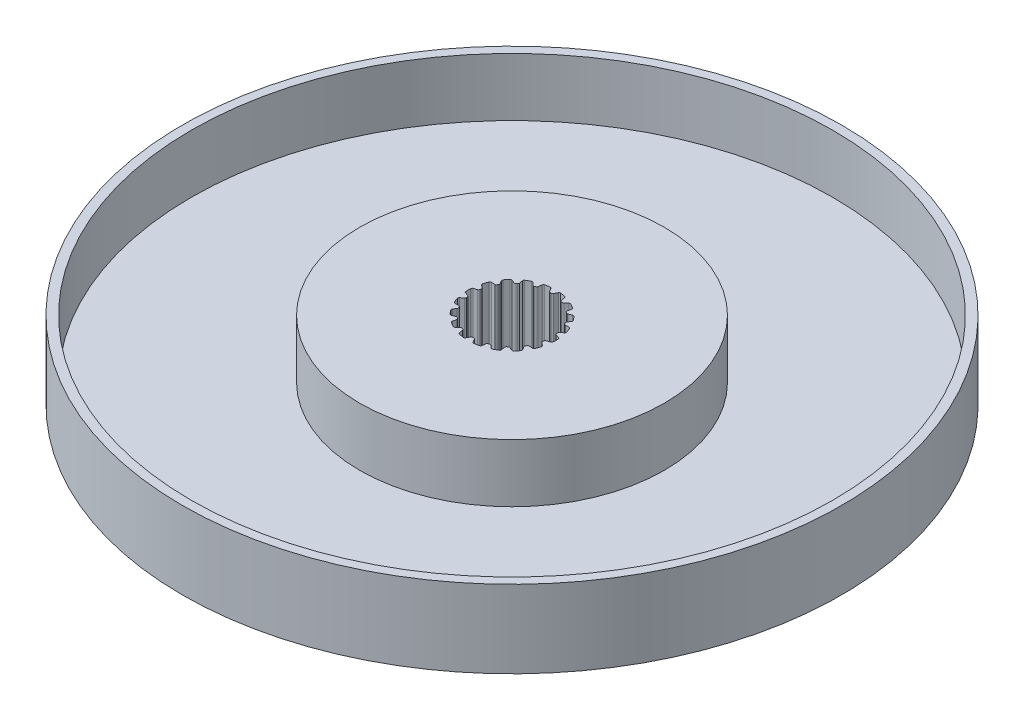
SolidWorks part; units mm, degrees
ref_plane "Front Plane" through (0, 0, 0) normal (0, 0, 1) x (1, 0, 0)
ref_plane "Top Plane" through (0, 0, 0) normal (0, 1, 0) x (1, 0, 0)
ref_plane "Right Plane" through (0, 0, 0) normal (1, 0, 0) x (0, 0, -1)
sketch "Sketch1" plane through (0, 0, 0) normal (0, 1, 0) x (1, 0, 0)
  circle A0 centre (0, 0) radius 42.5
  dimension "D1" = 85
extrude "Boss-Extrude1" add sketch "Sketch1" along normal blind 10
sketch "Sketch2" plane through (0, 10, 10) normal (0, 1, 0) x (1, 0, 0)
  line L1 (-5.2151, 8.5153) -> (-4.9419, 8.7287)
  line L3 (-5.0787, 9.5044) -> (-5.4084, 9.6115)
  line L5 (-5.4084, 10.3885) -> (-5.0787, 10.4956)
  line L7 (-4.9419, 11.2713) -> (-5.2151, 11.4847)
  line L9 (-4.9493, 12.2148) -> (-4.6029, 12.2027)
  line L11 (-4.2091, 12.8848) -> (-4.3928, 13.1788)
  line L13 (-3.8933, 13.774) -> (-3.5719, 13.6442)
  line L15 (-2.9686, 14.1504) -> (-3.0406, 14.4895)
  line L17 (-2.3677, 14.878) -> (-2.1101, 14.6461)
  line L19 (-1.37, 14.9154) -> (-1.3217, 15.2587)
  line L21 (-0.5566, 15.3937) -> (-0.3938, 15.0876)
  line L23 (0.3938, 15.0876) -> (0.5566, 15.3937)
  line L25 (1.3217, 15.2587) -> (1.37, 14.9154)
  line L27 (2.1101, 14.6461) -> (2.3677, 14.878)
  line L29 (3.0406, 14.4895) -> (2.9686, 14.1504)
  line L31 (3.5719, 13.6442) -> (3.8933, 13.774)
  line L33 (4.3928, 13.1788) -> (4.2091, 12.8848)
  line L35 (4.6029, 12.2027) -> (4.9493, 12.2148)
  line L37 (5.2151, 11.4847) -> (4.9419, 11.2713)
  line L39 (5.0787, 10.4956) -> (5.4084, 10.3885)
  line L41 (5.4084, 9.6115) -> (5.0787, 9.5044)
  line L43 (4.9419, 8.7287) -> (5.2151, 8.5153)
  line L45 (4.9493, 7.7852) -> (4.6029, 7.7973)
  line L47 (4.2091, 7.1152) -> (4.3928, 6.8212)
  line L49 (3.8933, 6.226) -> (3.5719, 6.3558)
  line L51 (2.9686, 5.8496) -> (3.0406, 5.5105)
  line L53 (2.3677, 5.122) -> (2.1101, 5.3539)
  line L55 (1.37, 5.0846) -> (1.3217, 4.7413)
  line L57 (0.5566, 4.6063) -> (0.3938, 4.9124)
  line L59 (-0.3938, 4.9124) -> (-0.5566, 4.6063)
  line L61 (-1.3217, 4.7413) -> (-1.37, 5.0846)
  line L63 (-2.1101, 5.3539) -> (-2.3677, 5.122)
  line L65 (-3.0406, 5.5105) -> (-2.9686, 5.8496)
  line L67 (-3.5719, 6.3558) -> (-3.8933, 6.226)
  line L69 (-4.3928, 6.8212) -> (-4.2091, 7.1152)
  line L71 (-4.6029, 7.7973) -> (-4.9493, 7.7852)
  circle A0 centre (0, 10) radius 42.5 construction
  arc A1 (-5.292, 8.2623) -> (-5.1709, 7.9295) centre (0, 10) ccw
  arc A3 (-5.2151, 8.5153) -> (-5.292, 8.2623) centre (-5.0735, 8.334) ccw
  arc A5 (-4.9419, 8.7287) -> (-4.8325, 9.0245) centre (-5.1266, 8.9651) ccw
  arc A7 (-4.8747, 9.2639) -> (-4.8325, 9.0245) centre (0, 10) ccw
  arc A9 (-4.8747, 9.2639) -> (-5.0787, 9.5044) centre (-5.1714, 9.2191) ccw
  arc A11 (-5.5672, 9.8229) -> (-5.4084, 9.6115) centre (-5.3373, 9.8302) ccw
  arc A13 (-5.5672, 10.1771) -> (-5.5672, 9.8229) centre (0, 10) ccw
  arc A15 (-5.4084, 10.3885) -> (-5.5672, 10.1771) centre (-5.3373, 10.1698) ccw
  arc A17 (-5.0787, 10.4956) -> (-4.8747, 10.7361) centre (-5.1714, 10.7809) ccw
  arc A19 (-4.8325, 10.9755) -> (-4.8747, 10.7361) centre (0, 10) ccw
  arc A21 (-4.8325, 10.9755) -> (-4.9419, 11.2713) centre (-5.1266, 11.0349) ccw
  arc A23 (-5.292, 11.7377) -> (-5.2151, 11.4847) centre (-5.0735, 11.666) ccw
  arc A25 (-5.1709, 12.0705) -> (-5.292, 11.7377) centre (0, 10) ccw
  arc A27 (-4.9493, 12.2148) -> (-5.1709, 12.0705) centre (-4.9574, 11.985) ccw
  arc A29 (-4.6029, 12.2027) -> (-4.329, 12.359) centre (-4.5924, 12.5026) ccw
  arc A31 (-4.2074, 12.5695) -> (-4.329, 12.359) centre (0, 10) ccw
  arc A33 (-4.2074, 12.5695) -> (-4.2091, 12.8848) centre (-4.4635, 12.7259) ccw
  arc A35 (-4.3785, 13.4429) -> (-4.3928, 13.1788) centre (-4.1977, 13.3007) ccw
  arc A37 (-4.1509, 13.7142) -> (-4.3785, 13.4429) centre (0, 10) ccw
  arc A39 (-3.8933, 13.774) -> (-4.1509, 13.7142) centre (-3.9795, 13.5608) ccw
  arc A41 (-3.5719, 13.6442) -> (-3.2611, 13.6973) centre (-3.4595, 13.9223) ccw
  arc A43 (-3.0749, 13.8536) -> (-3.2611, 13.6973) centre (0, 10) ccw
  arc A45 (-3.0749, 13.8536) -> (-2.9686, 14.1504) centre (-3.262, 14.0881) ccw
  arc A47 (-2.9369, 14.7328) -> (-3.0406, 14.4895) centre (-2.8157, 14.5374) ccw
  arc A49 (-2.6303, 14.9099) -> (-2.9369, 14.7328) centre (0, 10) ccw
  arc A51 (-2.3677, 14.878) -> (-2.6303, 14.9099) centre (-2.5216, 14.7071) ccw
  arc A53 (-2.1101, 14.6461) -> (-1.7998, 14.5897) centre (-1.9094, 14.869) ccw
  arc A55 (-1.5714, 14.6728) -> (-1.7998, 14.5897) centre (0, 10) ccw
  arc A57 (-1.5714, 14.6728) -> (-1.37, 14.9154) centre (-1.6671, 14.9572) ccw
  arc A59 (-1.1411, 15.4519) -> (-1.3217, 15.2587) centre (-1.094, 15.2267) ccw
  arc A61 (-0.7924, 15.5134) -> (-1.1411, 15.4519) centre (0, 10) ccw
  arc A63 (-0.5566, 15.3937) -> (-0.7924, 15.5134) centre (-0.7596, 15.2857) ccw
  arc A65 (-0.3938, 15.0876) -> (-0.1215, 14.9285) centre (-0.1289, 15.2284) ccw
  arc A67 (0.1215, 14.9285) -> (-0.1215, 14.9285) centre (0, 10) ccw
  arc A69 (0.1215, 14.9285) -> (0.3938, 15.0876) centre (0.1289, 15.2284) ccw
  arc A71 (0.7924, 15.5134) -> (0.5566, 15.3937) centre (0.7596, 15.2857) ccw
  arc A73 (1.1411, 15.4519) -> (0.7924, 15.5134) centre (0, 10) ccw
  arc A75 (1.3217, 15.2587) -> (1.1411, 15.4519) centre (1.094, 15.2267) ccw
  arc A77 (1.37, 14.9154) -> (1.5714, 14.6728) centre (1.6671, 14.9572) ccw
  arc A79 (1.7998, 14.5897) -> (1.5714, 14.6728) centre (0, 10) ccw
  arc A81 (1.7998, 14.5897) -> (2.1101, 14.6461) centre (1.9094, 14.869) ccw
  arc A83 (2.6303, 14.9099) -> (2.3677, 14.878) centre (2.5216, 14.7071) ccw
  arc A85 (2.9369, 14.7328) -> (2.6303, 14.9099) centre (0, 10) ccw
  arc A87 (3.0406, 14.4895) -> (2.9369, 14.7328) centre (2.8157, 14.5374) ccw
  arc A89 (2.9686, 14.1504) -> (3.0749, 13.8536) centre (3.262, 14.0881) ccw
  arc A91 (3.2611, 13.6973) -> (3.0749, 13.8536) centre (0, 10) ccw
  arc A93 (3.2611, 13.6973) -> (3.5719, 13.6442) centre (3.4595, 13.9223) ccw
  arc A95 (4.1509, 13.7142) -> (3.8933, 13.774) centre (3.9795, 13.5608) ccw
  arc A97 (4.3785, 13.4429) -> (4.1509, 13.7142) centre (0, 10) ccw
  arc A99 (4.3928, 13.1788) -> (4.3785, 13.4429) centre (4.1977, 13.3007) ccw
  arc A101 (4.2091, 12.8848) -> (4.2074, 12.5695) centre (4.4635, 12.7259) ccw
  arc A103 (4.329, 12.359) -> (4.2074, 12.5695) centre (0, 10) ccw
  arc A105 (4.329, 12.359) -> (4.6029, 12.2027) centre (4.5924, 12.5026) ccw
  arc A107 (5.1709, 12.0705) -> (4.9493, 12.2148) centre (4.9574, 11.985) ccw
  arc A109 (5.292, 11.7377) -> (5.1709, 12.0705) centre (0, 10) ccw
  arc A111 (5.2151, 11.4847) -> (5.292, 11.7377) centre (5.0735, 11.666) ccw
  arc A113 (4.9419, 11.2713) -> (4.8325, 10.9755) centre (5.1266, 11.0349) ccw
  arc A115 (4.8747, 10.7361) -> (4.8325, 10.9755) centre (0, 10) ccw
  arc A117 (4.8747, 10.7361) -> (5.0787, 10.4956) centre (5.1714, 10.7809) ccw
  arc A119 (5.5672, 10.1771) -> (5.4084, 10.3885) centre (5.3373, 10.1698) ccw
  arc A121 (5.5672, 9.8229) -> (5.5672, 10.1771) centre (0, 10) ccw
  arc A123 (5.4084, 9.6115) -> (5.5672, 9.8229) centre (5.3373, 9.8302) ccw
  arc A125 (5.0787, 9.5044) -> (4.8747, 9.2639) centre (5.1714, 9.2191) ccw
  arc A127 (4.8325, 9.0245) -> (4.8747, 9.2639) centre (0, 10) ccw
  arc A129 (4.8325, 9.0245) -> (4.9419, 8.7287) centre (5.1266, 8.9651) ccw
  arc A131 (5.292, 8.2623) -> (5.2151, 8.5153) centre (5.0735, 8.334) ccw
  arc A133 (5.1709, 7.9295) -> (5.292, 8.2623) centre (0, 10) ccw
  arc A135 (4.9493, 7.7852) -> (5.1709, 7.9295) centre (4.9574, 8.015) ccw
  arc A137 (4.6029, 7.7973) -> (4.329, 7.641) centre (4.5924, 7.4974) ccw
  arc A139 (4.2074, 7.4305) -> (4.329, 7.641) centre (0, 10) ccw
  arc A141 (4.2074, 7.4305) -> (4.2091, 7.1152) centre (4.4635, 7.2741) ccw
  arc A143 (4.3785, 6.5571) -> (4.3928, 6.8212) centre (4.1977, 6.6993) ccw
  arc A145 (4.1509, 6.2858) -> (4.3785, 6.5571) centre (0, 10) ccw
  arc A147 (3.8933, 6.226) -> (4.1509, 6.2858) centre (3.9795, 6.4392) ccw
  arc A149 (3.5719, 6.3558) -> (3.2611, 6.3027) centre (3.4595, 6.0777) ccw
  arc A151 (3.0749, 6.1464) -> (3.2611, 6.3027) centre (0, 10) ccw
  arc A153 (3.0749, 6.1464) -> (2.9686, 5.8496) centre (3.262, 5.9119) ccw
  arc A155 (2.9369, 5.2672) -> (3.0406, 5.5105) centre (2.8157, 5.4626) ccw
  arc A157 (2.6303, 5.0901) -> (2.9369, 5.2672) centre (0, 10) ccw
  arc A159 (2.3677, 5.122) -> (2.6303, 5.0901) centre (2.5216, 5.2929) ccw
  arc A161 (2.1101, 5.3539) -> (1.7998, 5.4103) centre (1.9094, 5.131) ccw
  arc A163 (1.5714, 5.3272) -> (1.7998, 5.4103) centre (0, 10) ccw
  arc A165 (1.5714, 5.3272) -> (1.37, 5.0846) centre (1.6671, 5.0428) ccw
  arc A167 (1.1411, 4.5481) -> (1.3217, 4.7413) centre (1.094, 4.7733) ccw
  arc A169 (0.7924, 4.4866) -> (1.1411, 4.5481) centre (0, 10) ccw
  arc A171 (0.5566, 4.6063) -> (0.7924, 4.4866) centre (0.7596, 4.7143) ccw
  arc A173 (0.3938, 4.9124) -> (0.1215, 5.0715) centre (0.1289, 4.7716) ccw
  arc A175 (-0.1215, 5.0715) -> (0.1215, 5.0715) centre (0, 10) ccw
  arc A177 (-0.1215, 5.0715) -> (-0.3938, 4.9124) centre (-0.1289, 4.7716) ccw
  arc A179 (-0.7924, 4.4866) -> (-0.5566, 4.6063) centre (-0.7596, 4.7143) ccw
  arc A181 (-1.1411, 4.5481) -> (-0.7924, 4.4866) centre (0, 10) ccw
  arc A183 (-1.3217, 4.7413) -> (-1.1411, 4.5481) centre (-1.094, 4.7733) ccw
  arc A185 (-1.37, 5.0846) -> (-1.5714, 5.3272) centre (-1.6671, 5.0428) ccw
  arc A187 (-1.7998, 5.4103) -> (-1.5714, 5.3272) centre (0, 10) ccw
  arc A189 (-1.7998, 5.4103) -> (-2.1101, 5.3539) centre (-1.9094, 5.131) ccw
  arc A191 (-2.6303, 5.0901) -> (-2.3677, 5.122) centre (-2.5216, 5.2929) ccw
  arc A193 (-2.9369, 5.2672) -> (-2.6303, 5.0901) centre (0, 10) ccw
  arc A195 (-3.0406, 5.5105) -> (-2.9369, 5.2672) centre (-2.8157, 5.4626) ccw
  arc A197 (-2.9686, 5.8496) -> (-3.0749, 6.1464) centre (-3.262, 5.9119) ccw
  arc A199 (-3.2611, 6.3027) -> (-3.0749, 6.1464) centre (0, 10) ccw
  arc A201 (-3.2611, 6.3027) -> (-3.5719, 6.3558) centre (-3.4595, 6.0777) ccw
  arc A203 (-4.1509, 6.2858) -> (-3.8933, 6.226) centre (-3.9795, 6.4392) ccw
  arc A205 (-4.3785, 6.5571) -> (-4.1509, 6.2858) centre (0, 10) ccw
  arc A207 (-4.3928, 6.8212) -> (-4.3785, 6.5571) centre (-4.1977, 6.6993) ccw
  arc A209 (-4.2091, 7.1152) -> (-4.2074, 7.4305) centre (-4.4635, 7.2741) ccw
  arc A211 (-4.329, 7.641) -> (-4.2074, 7.4305) centre (0, 10) ccw
  arc A213 (-4.329, 7.641) -> (-4.6029, 7.7973) centre (-4.5924, 7.4974) ccw
  arc A215 (-5.1709, 7.9295) -> (-4.9493, 7.7852) centre (-4.9574, 8.015) ccw
  dimension "D1" = 0
extrude "Cut-Extrude1" [suppressed] cut sketch "Sketch2" against normal blind 10
sketch "Sketch3" plane through (0, 10, 0) normal (0, 1, 0) x (1, 0, 0)
  circle A0 centre (0, 0) radius 19.65
  circle A1 centre (0, 0) radius 41.35
  dimension "D1" = 82.7
  dimension "D2" = 39.3
extrude "Cut-Extrude2" cut sketch "Sketch3" against normal blind 7.5
sketch "Sketch4" plane through (0, 10, 0) normal (0, 1, 0) x (1, 0, 0)
  line L0 (0, 0) -> (0, 6) construction
  line L1 (-0.4643, 5.5061) -> (-0.2516, 5.1061)
  line L2 (-0.075, 5) -> (0.075, 5)
  line L3 (0.2516, 5.1061) -> (0.4643, 5.5061)
  line L4 (0, 0) -> (-0.6644, 5.6108) construction
  line L5 (0, 0) -> (1.2947, 5.4997) construction
  line L6 (1.4469, 5.3328) -> (1.51, 4.8842)
  line L7 (1.6396, 4.7241) -> (1.7806, 4.6728)
  line L8 (1.9828, 4.7121) -> (2.3195, 5.0152)
  line L9 (3.1836, 4.5163) -> (3.0894, 4.0732)
  line L10 (3.1565, 3.8784) -> (3.2714, 3.782)
  line L11 (3.4749, 3.7498) -> (3.8949, 3.9195)
  line L12 (4.5363, 3.1551) -> (4.2962, 2.7709)
  line L13 (4.2926, 2.565) -> (4.3676, 2.435)
  line L14 (4.5478, 2.3352) -> (5.0005, 2.351)
  line L15 (5.3418, 1.4133) -> (4.9848, 1.1344)
  line L16 (4.911, 0.9421) -> (4.9371, 0.7944)
  line L17 (5.0722, 0.6389) -> (5.5031, 0.4989)
  line L18 (5.5031, -0.4989) -> (5.0722, -0.6389)
  line L19 (4.9371, -0.7944) -> (4.911, -0.9421)
  line L20 (4.9848, -1.1344) -> (5.3418, -1.4133)
  line L21 (5.0005, -2.351) -> (4.5478, -2.3352)
  line L22 (4.3676, -2.435) -> (4.2926, -2.565)
  line L23 (4.2962, -2.7709) -> (4.5363, -3.1551)
  line L24 (3.8949, -3.9195) -> (3.4749, -3.7498)
  line L25 (3.2714, -3.782) -> (3.1565, -3.8784)
  line L26 (3.0894, -4.0732) -> (3.1836, -4.5163)
  line L27 (2.3195, -5.0152) -> (1.9828, -4.7121)
  line L28 (1.7806, -4.6728) -> (1.6396, -4.7241)
  line L29 (1.51, -4.8842) -> (1.4469, -5.3328)
  line L30 (0.4643, -5.5061) -> (0.2516, -5.1061)
  line L31 (0.075, -5) -> (-0.075, -5)
  line L32 (-0.2516, -5.1061) -> (-0.4643, -5.5061)
  line L33 (-1.4469, -5.3328) -> (-1.51, -4.8842)
  line L34 (-1.6396, -4.7241) -> (-1.7806, -4.6728)
  line L35 (-1.9828, -4.7121) -> (-2.3195, -5.0152)
  line L36 (-3.1836, -4.5163) -> (-3.0894, -4.0732)
  line L37 (-3.1565, -3.8784) -> (-3.2714, -3.782)
  line L38 (-3.4749, -3.7498) -> (-3.8949, -3.9195)
  line L39 (-4.5363, -3.1551) -> (-4.2962, -2.7709)
  line L40 (-4.2926, -2.565) -> (-4.3676, -2.435)
  line L41 (-4.5478, -2.3352) -> (-5.0005, -2.351)
  line L42 (-5.3418, -1.4133) -> (-4.9848, -1.1344)
  line L43 (-4.911, -0.9421) -> (-4.9371, -0.7944)
  line L44 (-5.0722, -0.6389) -> (-5.5031, -0.4989)
  line L45 (-5.5031, 0.4989) -> (-5.0722, 0.6389)
  line L46 (-4.9371, 0.7944) -> (-4.911, 0.9421)
  line L47 (-4.9848, 1.1344) -> (-5.3418, 1.4133)
  line L48 (-5.0005, 2.351) -> (-4.5478, 2.3352)
  line L49 (-4.3676, 2.435) -> (-4.2926, 2.565)
  line L50 (-4.2962, 2.7709) -> (-4.5363, 3.1551)
  line L51 (-3.8949, 3.9195) -> (-3.4749, 3.7498)
  line L52 (-3.2714, 3.782) -> (-3.1565, 3.8784)
  line L53 (-3.0894, 4.0732) -> (-3.1836, 4.5163)
  line L54 (-2.3195, 5.0152) -> (-1.9828, 4.7121)
  line L55 (-1.7806, 4.6728) -> (-1.6396, 4.7241)
  line L56 (-1.51, 4.8842) -> (-1.4469, 5.3328)
  arc A1 (0.075, 5) -> (0.2516, 5.1061) centre (0.075, 5.2) ccw
  arc A2 (-0.2516, 5.1061) -> (-0.075, 5) centre (-0.075, 5.2) ccw
  arc A5 (-0.6644, 5.6108) -> (0.6644, 5.6108) centre (0, 0) ccw construction
  arc A6 (0.4643, 5.5061) -> (0.6644, 5.6108) centre (0.6409, 5.4122) cw
  arc A7 (-0.4643, 5.5061) -> (-0.6644, 5.6108) centre (-0.6409, 5.4122) ccw
  arc A8 (1.7806, 4.6728) -> (1.9828, 4.7121) centre (1.849, 4.8608) ccw
  arc A9 (1.51, 4.8842) -> (1.6396, 4.7241) centre (1.708, 4.9121) ccw
  arc A10 (2.3195, 5.0152) -> (2.5433, 5.0452) centre (2.4533, 4.8666) cw
  arc A11 (1.4469, 5.3328) -> (1.2947, 5.4997) centre (1.2489, 5.305) ccw
  arc A12 (3.2714, 3.782) -> (3.4749, 3.7498) centre (3.3999, 3.9352) ccw
  arc A13 (3.0894, 4.0732) -> (3.1565, 3.8784) centre (3.285, 4.0316) ccw
  arc A14 (3.8949, 3.9195) -> (4.1155, 3.8711) centre (3.9698, 3.734) cw
  arc A15 (3.1836, 4.5163) -> (3.0976, 4.7252) centre (2.988, 4.5579) ccw
  arc A16 (4.3676, 2.435) -> (4.5478, 2.3352) centre (4.5408, 2.535) ccw
  arc A17 (4.2962, 2.7709) -> (4.2926, 2.565) centre (4.4658, 2.665) ccw
  arc A18 (5.0005, 2.351) -> (5.1913, 2.23) centre (5.0075, 2.1511) cw
  arc A19 (4.5363, 3.1551) -> (4.5269, 3.3808) centre (4.3667, 3.2611) ccw
  arc A20 (4.9371, 0.7944) -> (5.0722, 0.6389) centre (5.134, 0.8291) ccw
  arc A21 (4.9848, 1.1344) -> (4.911, 0.9421) centre (5.108, 0.9768) ccw
  arc A22 (5.5031, 0.4989) -> (5.6409, 0.32) centre (5.4413, 0.3087) cw
  arc A23 (5.3418, 1.4133) -> (5.4102, 1.6286) centre (5.2187, 1.5709) ccw
  arc A24 (4.911, -0.9421) -> (4.9848, -1.1344) centre (5.108, -0.9768) ccw
  arc A25 (5.0722, -0.6389) -> (4.9371, -0.7944) centre (5.134, -0.8291) ccw
  arc A26 (5.3418, -1.4133) -> (5.4102, -1.6286) centre (5.2187, -1.5709) cw
  arc A27 (5.5031, -0.4989) -> (5.6409, -0.32) centre (5.4413, -0.3087) ccw
  arc A28 (4.2926, -2.565) -> (4.2962, -2.7709) centre (4.4658, -2.665) ccw
  arc A29 (4.5478, -2.3352) -> (4.3676, -2.435) centre (4.5408, -2.535) ccw
  arc A30 (4.5363, -3.1551) -> (4.5269, -3.3808) centre (4.3667, -3.2611) cw
  arc A31 (5.0005, -2.351) -> (5.1913, -2.23) centre (5.0075, -2.1511) ccw
  arc A32 (3.1565, -3.8784) -> (3.0894, -4.0732) centre (3.285, -4.0316) ccw
  arc A33 (3.4749, -3.7498) -> (3.2714, -3.782) centre (3.3999, -3.9352) ccw
  arc A34 (3.1836, -4.5163) -> (3.0976, -4.7252) centre (2.988, -4.5579) cw
  arc A35 (3.8949, -3.9195) -> (4.1155, -3.8711) centre (3.9698, -3.734) ccw
  arc A36 (1.6396, -4.7241) -> (1.51, -4.8842) centre (1.708, -4.9121) ccw
  arc A37 (1.9828, -4.7121) -> (1.7806, -4.6728) centre (1.849, -4.8608) ccw
  arc A38 (1.4469, -5.3328) -> (1.2947, -5.4997) centre (1.2489, -5.305) cw
  arc A39 (2.3195, -5.0152) -> (2.5433, -5.0452) centre (2.4533, -4.8666) ccw
  arc A40 (-0.075, -5) -> (-0.2516, -5.1061) centre (-0.075, -5.2) ccw
  arc A41 (0.2516, -5.1061) -> (0.075, -5) centre (0.075, -5.2) ccw
  arc A42 (-0.4643, -5.5061) -> (-0.6644, -5.6108) centre (-0.6409, -5.4122) cw
  arc A43 (0.4643, -5.5061) -> (0.6644, -5.6108) centre (0.6409, -5.4122) ccw
  arc A44 (-1.7806, -4.6728) -> (-1.9828, -4.7121) centre (-1.849, -4.8608) ccw
  arc A45 (-1.51, -4.8842) -> (-1.6396, -4.7241) centre (-1.708, -4.9121) ccw
  arc A46 (-2.3195, -5.0152) -> (-2.5433, -5.0452) centre (-2.4533, -4.8666) cw
  arc A47 (-1.4469, -5.3328) -> (-1.2947, -5.4997) centre (-1.2489, -5.305) ccw
  arc A48 (-3.2714, -3.782) -> (-3.4749, -3.7498) centre (-3.3999, -3.9352) ccw
  arc A49 (-3.0894, -4.0732) -> (-3.1565, -3.8784) centre (-3.285, -4.0316) ccw
  arc A50 (-3.8949, -3.9195) -> (-4.1155, -3.8711) centre (-3.9698, -3.734) cw
  arc A51 (-3.1836, -4.5163) -> (-3.0976, -4.7252) centre (-2.988, -4.5579) ccw
  arc A52 (-4.3676, -2.435) -> (-4.5478, -2.3352) centre (-4.5408, -2.535) ccw
  arc A53 (-4.2962, -2.7709) -> (-4.2926, -2.565) centre (-4.4658, -2.665) ccw
  arc A54 (-5.0005, -2.351) -> (-5.1913, -2.23) centre (-5.0075, -2.1511) cw
  arc A55 (-4.5363, -3.1551) -> (-4.5269, -3.3808) centre (-4.3667, -3.2611) ccw
  arc A56 (-4.9371, -0.7944) -> (-5.0722, -0.6389) centre (-5.134, -0.8291) ccw
  arc A57 (-4.9848, -1.1344) -> (-4.911, -0.9421) centre (-5.108, -0.9768) ccw
  arc A58 (-5.5031, -0.4989) -> (-5.6409, -0.32) centre (-5.4413, -0.3087) cw
  arc A59 (-5.3418, -1.4133) -> (-5.4102, -1.6286) centre (-5.2187, -1.5709) ccw
  arc A60 (-4.911, 0.9421) -> (-4.9848, 1.1344) centre (-5.108, 0.9768) ccw
  arc A61 (-5.0722, 0.6389) -> (-4.9371, 0.7944) centre (-5.134, 0.8291) ccw
  arc A62 (-5.3418, 1.4133) -> (-5.4102, 1.6286) centre (-5.2187, 1.5709) cw
  arc A63 (-5.5031, 0.4989) -> (-5.6409, 0.32) centre (-5.4413, 0.3087) ccw
  arc A64 (-4.2926, 2.565) -> (-4.2962, 2.7709) centre (-4.4658, 2.665) ccw
  arc A65 (-4.5478, 2.3352) -> (-4.3676, 2.435) centre (-4.5408, 2.535) ccw
  arc A66 (-4.5363, 3.1551) -> (-4.5269, 3.3808) centre (-4.3667, 3.2611) cw
  arc A67 (-5.0005, 2.351) -> (-5.1913, 2.23) centre (-5.0075, 2.1511) ccw
  arc A68 (-3.1565, 3.8784) -> (-3.0894, 4.0732) centre (-3.285, 4.0316) ccw
  arc A69 (-3.4749, 3.7498) -> (-3.2714, 3.782) centre (-3.3999, 3.9352) ccw
  arc A70 (-3.1836, 4.5163) -> (-3.0976, 4.7252) centre (-2.988, 4.5579) cw
  arc A71 (-3.8949, 3.9195) -> (-4.1155, 3.8711) centre (-3.9698, 3.734) ccw
  arc A72 (-1.6396, 4.7241) -> (-1.51, 4.8842) centre (-1.708, 4.9121) ccw
  arc A73 (-1.9828, 4.7121) -> (-1.7806, 4.6728) centre (-1.849, 4.8608) ccw
  arc A74 (-1.4469, 5.3328) -> (-1.2947, 5.4997) centre (-1.2489, 5.305) cw
  arc A75 (-2.3195, 5.0152) -> (-2.5433, 5.0452) centre (-2.4533, 4.8666) ccw
  arc A76 (0.6644, 5.6108) -> (1.2947, 5.4997) centre (0, 0) cw
  arc A77 (2.5433, 5.0452) -> (3.0976, 4.7252) centre (0, 0) cw
  arc A78 (4.1155, 3.8711) -> (4.5269, 3.3808) centre (0, 0) cw
  arc A79 (5.1913, 2.23) -> (5.4102, 1.6286) centre (0, 0) cw
  arc A80 (5.6409, 0.32) -> (5.6409, -0.32) centre (0, 0) cw
  arc A81 (5.4102, -1.6286) -> (5.1913, -2.23) centre (0, 0) cw
  arc A82 (4.5269, -3.3808) -> (4.1155, -3.8711) centre (0, 0) cw
  arc A83 (3.0976, -4.7252) -> (2.5433, -5.0452) centre (0, 0) cw
  arc A84 (1.2947, -5.4997) -> (0.6644, -5.6108) centre (0, 0) cw
  arc A85 (-0.6644, -5.6108) -> (-1.2947, -5.4997) centre (0, 0) cw
  arc A86 (-2.5433, -5.0452) -> (-3.0976, -4.7252) centre (0, 0) cw
  arc A87 (-4.1155, -3.8711) -> (-4.5269, -3.3808) centre (0, 0) cw
  arc A88 (-5.1913, -2.23) -> (-5.4102, -1.6286) centre (0, 0) cw
  arc A89 (-5.6409, -0.32) -> (-5.6409, 0.32) centre (0, 0) cw
  arc A90 (-5.4102, 1.6286) -> (-5.1913, 2.23) centre (0, 0) cw
  arc A91 (-4.5269, 3.3808) -> (-4.1155, 3.8711) centre (0, 0) cw
  arc A92 (-3.0976, 4.7252) -> (-2.5433, 5.0452) centre (0, 0) cw
  arc A93 (-1.2947, 5.4997) -> (-0.6644, 5.6108) centre (0, 0) cw
  point P14 (0.1952, 5)
  point P17 (-0.1952, 5)
  point P225 (0, 0)
  point P260 (0, 0)
  dimension "D6" = 0.2
  dimension "D7" = 11.3
  dimension "D10" = 0.2
  dimension "D2" = 28
  dimension "D3" = 28
  dimension "D8" = 0.15
  dimension "D9" = 20
  dimension "D4" = 0.075
  dimension "D5" = 5
  dimension "D12" = 18
  dimension "D11" = 18
extrude "Cut-Extrude4" cut sketch "Sketch4" against normal through all contours A93 A74 L56 A72 L55 A73 L54 A75 A92 A70 L53 A68 L52 A69 L51 A71 A91 A66 L50 A64 L49 A65 L48 A67 A90 A62 L47 A60 L46 A61 L45 A63 A89 A58 L44 A56 L43 A57 L42 A59 A88 A54 L41 A52 L40 A53 L39 A55 A87 A50 L38
sketch "Sketch5" plane through (0, 10, 0) normal (0, 1, 0) x (1, 0, 0)
  circle A0 centre (0, 0) radius 7.5
  circle A1 centre (0, 0) radius 50
  dimension "D1" = 100
  dimension "D2" = 15
extrude "Cut-Extrude5" [suppressed] cut sketch "Sketch5" against normal through all
equation "\"D4@Sketch4\"=\"D8@Sketch4\"/2"
